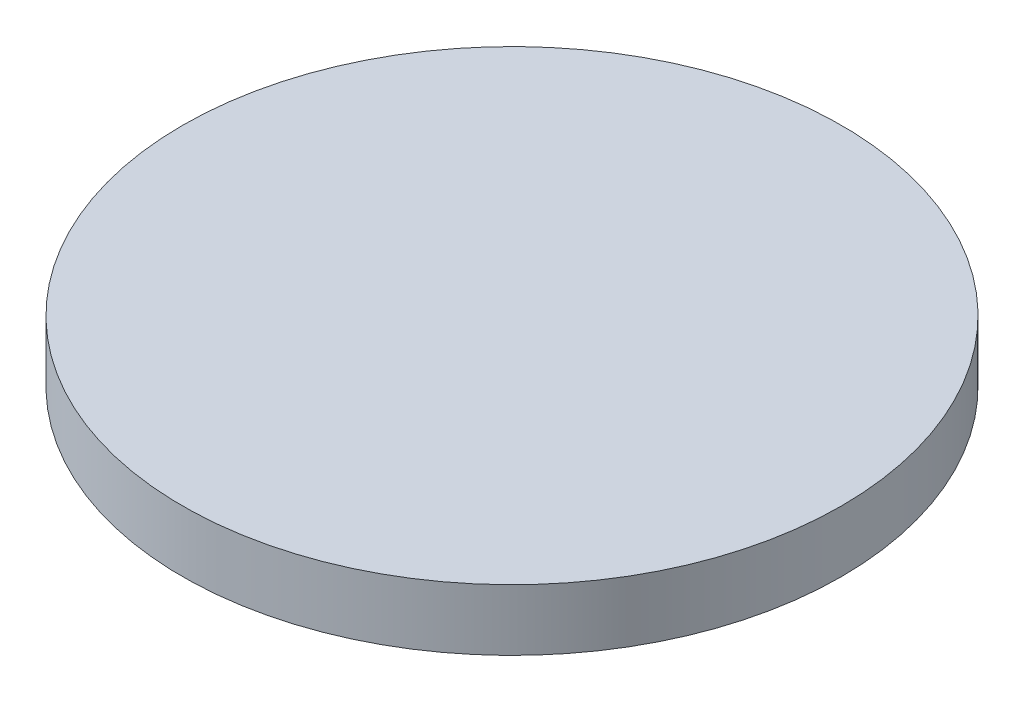
SolidWorks part; units mm, degrees
material "Glass"
ref_plane "Front Plane" through (0, 0, 0) normal (0, 0, 1) x (1, 0, 0)
ref_plane "Top Plane" through (0, 0, 0) normal (0, 1, 0) x (1, 0, 0)
ref_plane "Right Plane" through (0, 0, 0) normal (1, 0, 0) x (0, 0, -1)
sketch "Sketch2" plane through (0, 0, 0) normal (0, 0, 1) x (1, 0, 0)
  line L0 (0, -815.8479) -> (0, -1012.2957) construction
  line L2 (0, 0) -> (34.163, 0)
  line L3 (0, 0) -> (0, -6.35)
  line L4 (0, -6.35) -> (34.163, -6.35)
  line L5 (34.163, 0) -> (34.163, -6.35)
  dimension "D1" = 6.35
  dimension "D2" = 34.163
revolve "Revolve2" add sketch "Sketch2" angle 360 about L0
